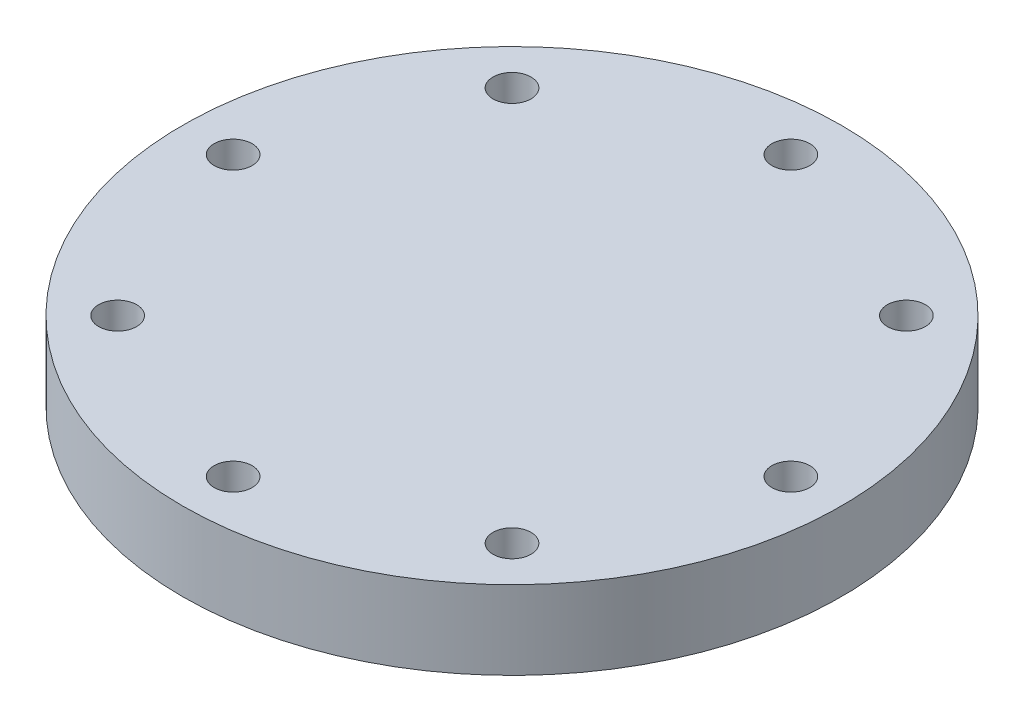
SolidWorks part; units mm, degrees
ref_plane "Front Plane" through (0, 0, 0) normal (0, 0, 1) x (1, 0, 0)
ref_plane "Top Plane" through (0, 0, 0) normal (0, 1, 0) x (1, 0, 0)
ref_plane "Right Plane" through (0, 0, 0) normal (1, 0, 0) x (0, 0, -1)
sketch "Sketch1" plane through (0, 0, 0) normal (0, 1, 0) x (1, 0, 0)
  circle A0 centre (0, 0) radius 26
  circle A1 centre (0, 22) radius 1.5
  dimension "D1" = 52
  dimension "D2" = 22
extrude "Boss-Extrude1" add sketch "Sketch1" along normal blind 6.2 contours A0
sketch "Sketch4" plane through (0, 0, 0) normal (0, -1, 0) x (1, 0, 0)
  circle A0 centre (22, 0) radius 1.5
  dimension "D1" = 22
extrude "Cut-Extrude1" cut sketch "Sketch4" against normal blind 13
sketch "Sketch5" plane through (0, 0, 0) normal (0, -1, 0) x (1, 0, 0)
  circle A0 centre (-22, 0) radius 1.5
  circle A1 centre (0, 22) radius 1.5
  circle A2 centre (0, -22) radius 1.5
  circle A3 centre (-15.5563, 15.5563) radius 1.5
  circle A4 centre (15.5563, 15.5563) radius 1.5
  circle A5 centre (15.5563, -15.5563) radius 1.5
  circle A6 centre (-15.5563, -15.5563) radius 1.5
  dimension "D4" = 22
  dimension "D1" = 22
  dimension "D2" = 22
  dimension "D3" = 22
  dimension "D5" = 22
  dimension "D6" = 22
  dimension "D7" = 22
extrude "Cut-Extrude2" cut sketch "Sketch5" against normal blind 10
sketch "Sketch6" plane through (0, 0, 0) normal (0, -1, 0) x (-1, 0, 0)
  text T0 "97"
  point P1 (-2.6924, -10.8584)
  point P2 (-7.9476, -15.8602)
  point P3 (0, 0)
extrude "Cut-Extrude3" cut sketch "Sketch6" against normal blind 1
